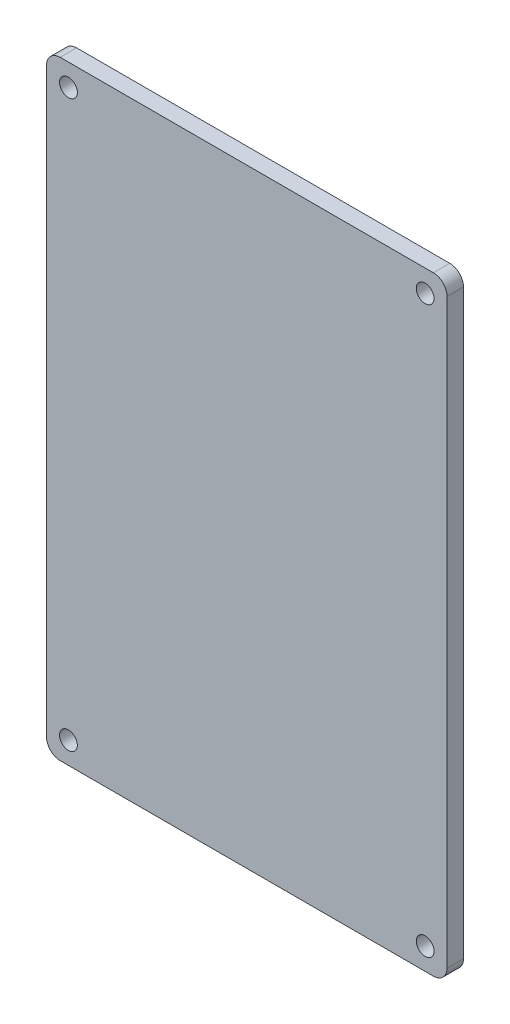
SolidWorks part; units mm, degrees
material "有机玻璃 (TM) GS 丙烯酸铸钣"
ref_plane "前视基准面" through (0, 0, 0) normal (0, 0, 1) x (1, 0, 0)
ref_plane "上视基准面" through (0, 0, 0) normal (0, 1, 0) x (1, 0, 0)
ref_plane "右视基准面" through (0, 0, 0) normal (1, 0, 0) x (0, 0, -1)
sketch "Model" plane through (0, 0, 0) normal (0, 0, 1) x (1, 0, 0)
  line L0 (73.1521, 8.0001) -> (73.1521, 108.7499)
  line L1 (8.0018, 111.2499) -> (70.6521, 111.2499)
  line L2 (65.1521, 0.0001) -> (2.5018, 0.0001)
  line L3 (0.0018, 8.0001) -> (0.0018, 108.7499)
  line L4 (8.0018, 111.2499) -> (2.5018, 111.2499)
  line L5 (0.0018, 8.0001) -> (0.0018, 2.5001)
  line L6 (65.1521, 0.0001) -> (70.6521, 0.0001)
  line L7 (73.1521, 8.0001) -> (73.1521, 2.5001)
  arc A0 (0.0018, 2.5001) -> (2.5018, 0.0001) centre (2.5018, 2.5001) ccw
  arc A1 (70.6521, 0.0001) -> (73.1521, 2.5001) centre (70.6521, 2.5001) ccw
  arc A2 (73.1521, 108.7499) -> (70.6521, 111.2499) centre (70.6521, 108.7499) ccw
  arc A3 (2.5018, 111.2499) -> (0.0018, 108.7499) centre (2.5018, 108.7499) ccw
  circle A4 centre (69.1521, 107.2499) radius 1.625
  circle A5 centre (4.0018, 107.2499) radius 1.625
  circle A6 centre (4.0018, 4.0001) radius 1.625
  circle A7 centre (69.1521, 4.0001) radius 1.625
extrude "凸台-拉伸2" add sketch "Model" along normal blind 3
